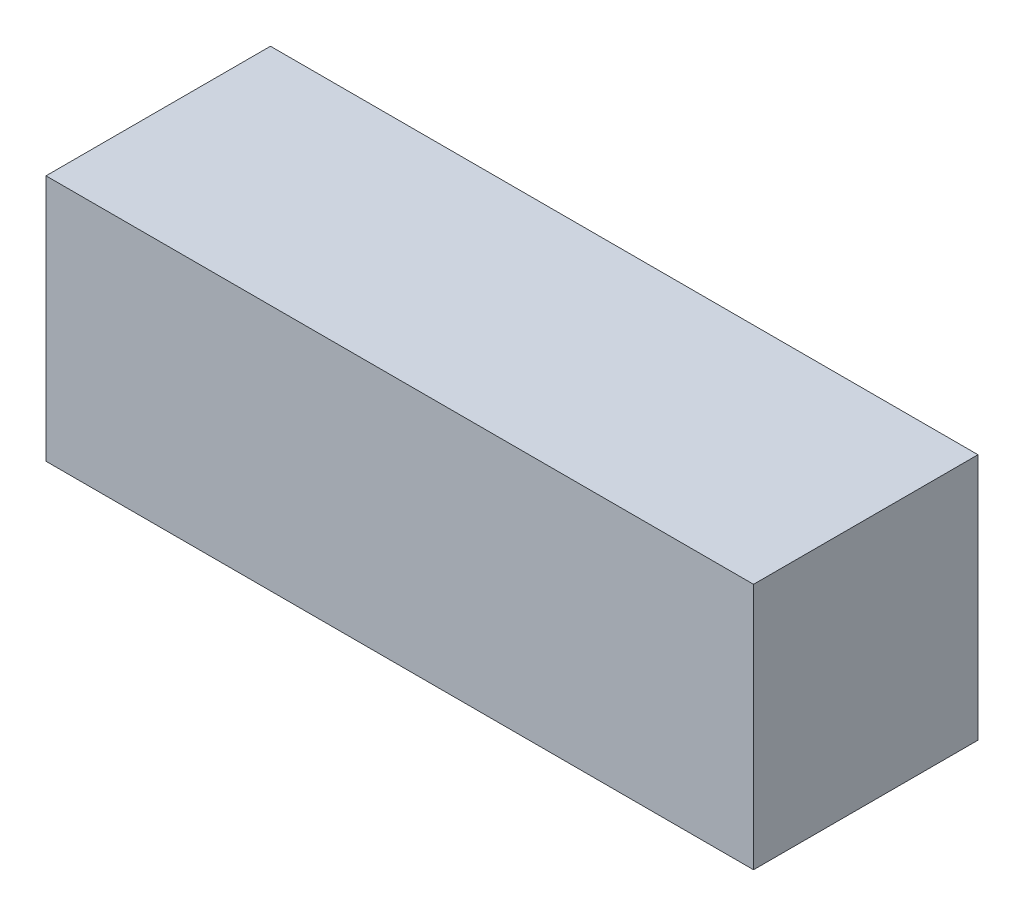
SolidWorks part; units mm, degrees
ref_plane "Front Plane" through (0, 0, 0) normal (0, 0, 1) x (1, 0, 0)
ref_plane "Top Plane" through (0, 0, 0) normal (0, 1, 0) x (1, 0, 0)
ref_plane "Right Plane" through (0, 0, 0) normal (1, 0, 0) x (0, 0, -1)
other "Bounding Box"
ref_plane "Default Plane" through (-8.9266, -12.7485, 0) normal (-0.1736, 0.9848, 0) x (0.9848, 0.1736, 0)
sketch "Sketch1" plane through (0, 0, 0) normal (0, 1, 0) x (1, 0, 0)
  line L1 (-26.8224, -8.509) -> (26.8224, -8.509)
  line L2 (-26.8224, -8.509) -> (-26.8224, 8.509)
  line L3 (-26.8224, 8.509) -> (26.8224, 8.509)
  line L4 (26.8224, -8.509) -> (26.8224, 8.509)
  line L5 (-26.8224, -8.509) -> (26.8224, 8.509) construction
  line L6 (-26.8224, 8.509) -> (26.8224, -8.509) construction
  point P0 (0, 0)
  dimension "D1" = 17.018
  dimension "D2" = 53.6448
extrude "Boss-Extrude1" add sketch "Sketch1" along normal blind 18.7452
